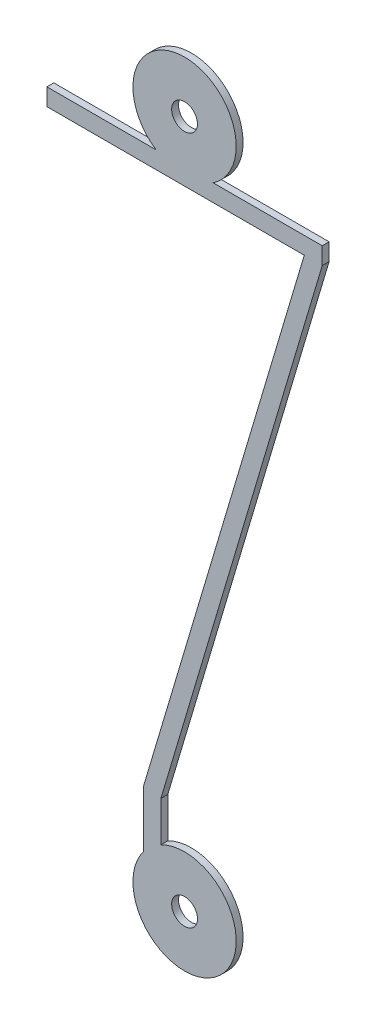
SolidWorks part; units mm, degrees
material "3.0517 (EN-AW 3003)"
ref_plane "Front Plane" through (0, 0, 0) normal (0, 0, 1) x (1, 0, 0)
ref_plane "Top Plane" through (0, 0, 0) normal (0, 1, 0) x (1, 0, 0)
ref_plane "Right Plane" through (0, 0, 0) normal (1, 0, 0) x (0, 0, -1)
sketch "Sketch1" plane through (0, 0, 0) normal (0, 0, 1) x (1, 0, 0)
  line L0 (0, 10) -> (0, -10) construction
  line L1 (-4, 8.75) -> (-0.8292, 8.75)
  line L2 (-4, 8.75) -> (-4, 8.25)
  line L3 (-4, 8.25) -> (3.4783, 8.25)
  line L4 (4, 8.75) -> (4, 8.25)
  line L5 (-0.6875, -8.6668) -> (-0.6875, -7.5)
  line L6 (-0.6875, -10) -> (-1.1875, -10) construction
  line L7 (-1.1875, -9.0836) -> (-1.1875, -7.4272)
  line L8 (-0.375, -10) -> (-0.6875, -10) construction
  line L9 (-1.1875, -10) -> (-1.5, -10) construction
  line L10 (0, -8.5) -> (-0.6875, -8.5) construction
  line L11 (4, 8.25) -> (-0.6875, -7.5)
  line L12 (3.4783, 8.25) -> (-1.1875, -7.4272)
  line L13 (3.5208, 8.3926) -> (-1.1667, -7.3574) construction
  line L14 (0.8292, 8.75) -> (4, 8.75)
  arc A0 (0.8292, 8.75) -> (-0.8292, 8.75) centre (0, 10) ccw
  circle A1 centre (0, 10) radius 0.375
  arc A2 (-1.1875, -9.0836) -> (-0.6875, -8.6668) centre (0, -10) ccw
  circle A3 centre (0, -10) radius 0.375
  point P3 (0, 0)
  dimension "D2" = 3
  dimension "D3" = 0.75
  dimension "D4" = 8
  dimension "D5" = 1.25
  dimension "D1" = 20
  dimension "D6" = 0.5
  dimension "D7" = 1
  dimension "D8" = 0.5
extrude "Boss-Extrude1" add sketch "Sketch1" along normal mid plane 0.2
sketch "Sketch2" plane through (0, 0, 0) normal (0, 0, 1) x (1, 0, 0)
  line L9 (-1.4375, -9.5715) -> (-0.4375, -8.5652)
  line L18 (-1.4361, 9) -> (-4.25, 9)
  line L19 (-4.25, 9) -> (-4.25, 8)
  line L20 (-4.25, 8) -> (3.1431, 8)
  line L21 (3.1431, 8) -> (-1.4375, -7.3908)
  line L22 (-1.4375, -7.3908) -> (-1.4375, -9.002)
  line L23 (-0.4375, -8.3056) -> (-0.4375, -7.5364)
  line L24 (-0.4375, -7.5364) -> (4.25, 8.2136)
  line L25 (4.25, 8.2136) -> (4.25, 9)
  line L26 (4.25, 9) -> (1.4361, 9)
  line L27 (0, 9) -> (-4.25, 9)
  line L28 (-4.25, 9) -> (-4.25, 8)
  line L29 (-4.25, 8) -> (3.1431, 8)
  line L30 (3.1431, 8) -> (-1.4375, -7.3908)
  line L31 (-1.4375, -7.3908) -> (-1.4375, -9.5715)
  line L32 (-0.4375, -8.5652) -> (-0.4375, -7.5364)
  line L33 (-0.4375, -7.5364) -> (4.25, 8.2136)
  line L34 (4.25, 8.2136) -> (4.25, 9)
  line L35 (4.25, 9) -> (0, 9)
  arc A2 (-1.1875, -9.0836) -> (-0.6875, -8.6668) centre (0, -10) ccw construction
  arc A3 (-1.1875, -9.0836) -> (-0.6875, -8.6668) centre (0, -10) ccw construction
  arc A4 (1.4361, 9) -> (-1.4361, 9) centre (0, 10) ccw
  arc A5 (-1.4375, -9.002) -> (-0.4375, -8.3056) centre (0, -10) ccw
  dimension "D1" = 0.25
extrude "Boss-Extrude2" [suppressed] add sketch "Sketch2" along normal mid plane 0.6
